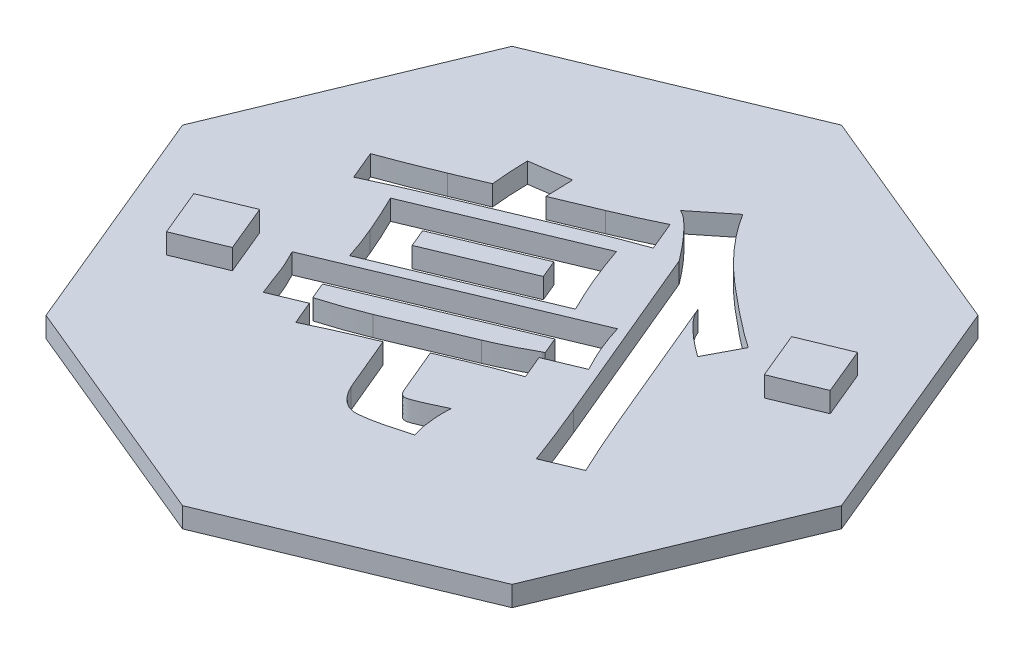
SolidWorks part; units mm, degrees
ref_plane "前视基准面" through (0, 0, 0) normal (0, 0, 1) x (1, 0, 0)
ref_plane "上视基准面" through (0, 0, 0) normal (0, 1, 0) x (1, 0, 0)
ref_plane "右视基准面" through (0, 0, 0) normal (1, 0, 0) x (0, 0, -1)
other "Configuration Table"
sketch "草图1" plane through (0, 0, 0) normal (0, 1, 0) x (1, 0, 0)
  line L15 (32.6641, 0) -> (23.097, 23.097)
  line L16 (23.097, 23.097) -> (0, 32.6641)
  line L17 (0, 32.6641) -> (-23.097, 23.097)
  line L18 (-23.097, 23.097) -> (-32.6641, 0)
  line L19 (-32.6641, 0) -> (-23.097, -23.097)
  line L20 (-23.097, -23.097) -> (0, -32.6641)
  line L21 (0, -32.6641) -> (23.097, -23.097)
  line L22 (23.097, -23.097) -> (32.6641, 0)
  circle A0 centre (0, 0) radius 30.1777 construction
  dimension "D1" = 25
extrude "凸台-拉伸1" add sketch "草图1" along normal blind 2
ref_plane "基准面1" through (0, 0, 0) normal (0, -1, 0) x (-1, 0, 0)
sketch "草图2" plane through (0, 0, 0) normal (0, -1, 0) x (-1, 0, 0)
  line L0 (0, 32.6641) -> (-23.097, -23.097) construction
  line L1 (11.5485, 27.8805) -> (-11.5485, -27.8805) construction
  line L2 (0, 32.6641) -> (23.097, 23.097) construction
  line L3 (0, -32.6641) -> (-23.097, -23.097) construction
  line L4 (-32.6525, 0.0279) -> (23.1085, -23.0691) construction
  line L7 (-23.097, 23.097) -> (32.6641, 0) construction
  text T0 "<b>停</b>" font "黑体" height 24
extrude "切除-拉伸1" cut sketch "草图2" against normal blind 2
ref_plane "基准面2" through (0, 2, 0) normal (0, 1, 0) x (1, 0, 0)
sketch "草图3" plane through (0, 2, 0) normal (0, 1, 0) x (1, 0, 0)
  line L0 (-27.8805, -11.5485) -> (27.8805, 11.5485) construction
  line L1 (-32.6641, 0) -> (-23.097, -23.097) construction
  line L2 (32.6641, 0) -> (23.097, 23.097) construction
sketch "草图4" plane through (0, 2, 0) normal (0, 1, 0) x (1, 0, 0)
  line L0 (-24.2178, -7.3254) -> (-22.3044, -11.9448)
  line L1 (-22.3044, -11.9448) -> (-17.685, -10.0314)
  line L2 (-17.685, -10.0314) -> (-19.5984, -5.412)
  line L4 (-19.5984, -5.412) -> (-22.3044, -11.9448) construction
  line L5 (-24.2178, -7.3254) -> (-17.685, -10.0314) construction
  line L6 (-27.8805, -11.5485) -> (27.8805, 11.5485) construction
  line L14 (-32.6641, 0) -> (-23.097, -23.097) construction
  line L15 (-32.6641, 0) -> (-23.097, -23.097) construction
  line L19 (-19.5984, -5.412) -> (-24.2178, -7.3254)
  line L22 (0, 35.6118) -> (0, -34.7752) construction
  line L23 (-23.097, 23.097) -> (23.097, -23.097) construction
  line L24 (-18.6887, 45.1185) -> (0, 0) construction
  line L25 (19.5984, 5.412) -> (17.685, 10.0314)
  line L26 (24.2178, 7.3254) -> (19.5984, 5.412)
  line L27 (22.3044, 11.9448) -> (24.2178, 7.3254)
  line L28 (17.685, 10.0314) -> (22.3044, 11.9448)
  point P2 (-20.9514, -8.6784)
  dimension "D1" = 5
  dimension "D2" = 5
  dimension "D3" = 5
  dimension "D4" = 45
  dimension "D5" = 22.5
  dimension "D6" = 40.3553
extrude "凸台-拉伸2" add sketch "草图4" along normal blind 2
ref_plane "基准面3" through (0, 0, 0) normal (0, -1, 0) x (-1, 0, 0)
sketch "草图5" plane through (0, 0, 0) normal (0, -1, 0) x (-1, 0, 0)
  line L0 (14.3057, -10.3482) -> (11.1192, -9.0174) construction
  line L1 (11.1192, -9.0174) -> (12.0861, -6.7042) construction
  line L2 (11.3635, -8.3365) -> (10.116, -11.3202) construction
  line L3 (-5.1199, -2.2182) -> (-8.4363, -0.8355) construction
  line L4 (-5.9308, -4.6042) -> (-4.6833, -1.6204) construction
  line L5 (-4.153, 0.095) -> (-5.1199, -2.2182) construction
  line L6 (14.3057, -10.3482) -> (11.1192, -9.0174) construction
  line L7 (11.1192, -9.0174) -> (12.0861, -6.7042) construction
  line L8 (11.3635, -8.3365) -> (10.116, -11.3202) construction
  line L9 (-5.1199, -2.2182) -> (-8.4363, -0.8355) construction
  line L10 (-5.9308, -4.6042) -> (-4.6833, -1.6204) construction
  line L11 (-4.153, 0.095) -> (-5.1199, -2.2182) construction
  line L12 (-4.6833, -1.6204) -> (-4.996, -1.4897)
  line L13 (-4.996, -1.4897) -> (-5.2731, -2.1544)
  line L14 (-5.2731, -2.1544) -> (-4.9611, -2.2848)
  line L15 (-4.9611, -2.2848) -> (-4.6833, -1.6204)
  line L16 (11.3635, -8.3365) -> (11.7405, -8.4941)
  line L17 (11.7405, -8.4941) -> (11.4621, -9.1606)
  line L18 (11.4621, -9.1606) -> (11.0849, -9.0029)
  line L19 (11.0849, -9.0029) -> (11.3635, -8.3365)
  spline S0 degree 3 poles (-781.0049, -1844.4738) (-26.5966, 37.3851) (-14.4361, 0.8877) (9.0052, -7.5825) (43.3046, -18.879) (85.0883, -5.2331) (-489.6686, -1943.5299) knots -15.406037 -15.406037 -15.406037 -15.406037 0.219457 0.459233 0.719135 23.585768 23.585768 23.585768 23.585768 only from (6.9867, -6.8134) to (11.3635, -8.3365) construction
  spline S1 degree 3 poles (-1010.2855, -1729.863) (-31.8748, 50.5882) (-25.5137, 8.8501) (-2.6256, -2.7156) (19.0488, -13.1722) (54.2972, 7.2592) (-762.753, -1852.2562) knots -16.128579 -16.128579 -16.128579 -16.128579 0.260523 0.514218 0.760802 16.109222 16.109222 16.109222 16.109222 only from (-4.6833, -1.6204) to (-0.6027, -3.6373) construction
  spline S2 degree 3 poles (6.9867, -6.8134) (7.3013, -6.94) (7.9598, -7.2048) (9.0052, -7.5825) (10.1509, -7.9599) (10.949, -8.2077) (11.3635, -8.3365) knots 0 0 0 0 0.219457 0.459233 0.719135 1 1 1 1 construction
  spline S3 degree 3 poles (-4.6833, -1.6204) (-4.338, -1.8135) (-3.6566, -2.1946) (-2.6256, -2.7156) (-1.6143, -3.2035) (-0.9365, -3.4942) (-0.6027, -3.6373) knots 0 0 0 0 0.260523 0.514218 0.760802 1 1 1 1 construction
extrude "切除-拉伸2" cut sketch "草图5" against normal blind 2
